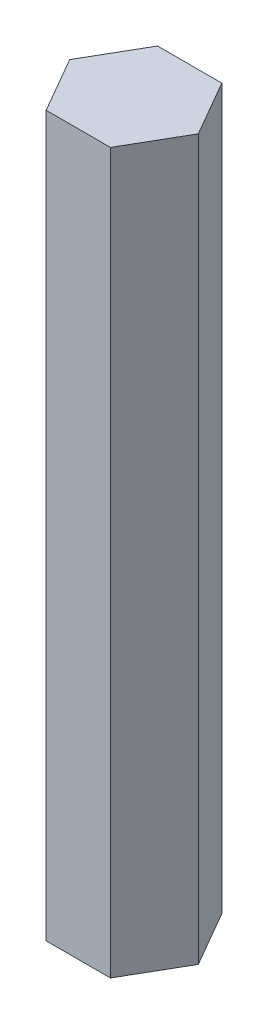
SolidWorks part; units mm, degrees
ref_plane "Front Plane" through (0, 0, 0) normal (0, 0, 1) x (1, 0, 0)
ref_plane "Top Plane" through (0, 0, 0) normal (0, 1, 0) x (1, 0, 0)
ref_plane "Right Plane" through (0, 0, 0) normal (1, 0, 0) x (0, 0, -1)
sketch "Sketch1" plane through (0, 0, 0) normal (0, 1, 0) x (1, 0, 0)
  line L1 (7.9771, 1.5793) -> (3.9771, 8.5075)
  line L2 (3.9771, 8.5075) -> (-4.0229, 8.5075)
  line L3 (-4.0229, 8.5075) -> (-8.0229, 1.5793)
  line L4 (-8.0229, 1.5793) -> (-4.0229, -5.3489)
  line L5 (-4.0229, -5.3489) -> (3.9771, -5.3489)
  line L6 (3.9771, -5.3489) -> (7.9771, 1.5793)
  circle A0 centre (-0.0229, 1.5793) radius 6.9282 construction
  dimension "D1" = 8
extrude "Boss-Extrude1" add sketch "Sketch1" along normal blind 89.5
